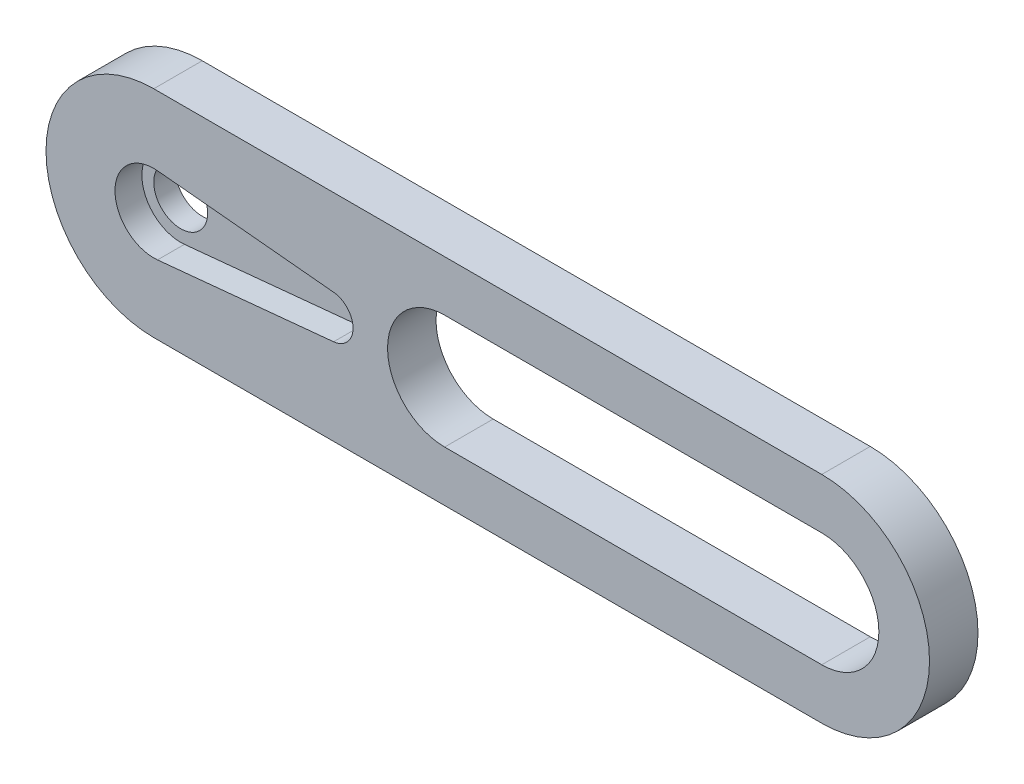
SolidWorks part; units mm, degrees
ref_plane "Front Plane" through (0, 0, 0) normal (0, 0, 1) x (1, 0, 0)
ref_plane "Top Plane" through (0, 0, 0) normal (0, 1, 0) x (1, 0, 0)
ref_plane "Right Plane" through (0, 0, 0) normal (1, 0, 0) x (0, 0, -1)
sketch "Esquisse1" plane through (0, 0, 0) normal (0, 0, 1) x (1, 0, 0)
  line L0 (-3.6, 0) -> (-3.6, 5.3986) construction
  line L1 (0.3491, 3.583) -> (16.6939, 1.9906)
  line L2 (16.6939, -1.9906) -> (0.3491, -3.583)
  line L3 (18.5, 0) -> (18.5, 4.9554) construction
  line L4 (0, 10) -> (62, 10)
  line L5 (0, -10) -> (62, -10)
  line L6 (27, 0) -> (62, 0) construction
  line L7 (27, 5.3) -> (62, 5.3)
  line L8 (27, -5.3) -> (62, -5.3)
  arc A0 (0.3491, 3.583) -> (0.3491, -3.583) centre (0, 0) ccw
  arc A1 (16.6939, -1.9906) -> (16.6939, 1.9906) centre (16.5, 0) ccw
  arc A2 (27, 5.3) -> (27, -5.3) centre (27, 0) ccw
  arc A3 (0, -10) -> (0, 10) centre (0, 0) cw
  arc A4 (62, 10) -> (62, -10) centre (62, 0) cw
  arc A5 (62, -5.3) -> (62, 5.3) centre (62, 0) ccw
  point P15 (44.5, 0)
  dimension "D2" = 3.6
  dimension "D3" = 2
  dimension "D5" = 35
  dimension "D6" = 10
  dimension "D8" = 10
  dimension "D4" = 5.3
  dimension "D1" = 22.1
  dimension "D7" = 62
extrude "Main" add sketch "Esquisse1" along normal blind 2.5
sketch "Esquisse2" plane through (0, 0, 0) normal (0, 0, -1) x (-1, 0, 0)
  line L0 (0, -10) -> (-62, -10)
  line L2 (0, -10) -> (-62, -10) construction
  line L3 (0, 10) -> (-62, 10)
  arc A0 (-62, 10) -> (-62, -10) centre (-62, 0) ccw construction
  circle A2 centre (0, 0) radius 2.5
  arc A3 (0, -10) -> (0, 10) centre (0, 0) ccw
  arc A5 (-62, 10) -> (-62, -10) centre (-62, 0) ccw
  dimension "D1" = 5
extrude "OriginalBracket" add sketch "Esquisse2" along normal blind 2
sketch "Sketch1" plane through (0, 0, 0) normal (0, 0, 1) x (1, 0, 0)
  line L0 (27, 0) -> (62, 0) construction
  line L1 (27, 5.3) -> (62, 5.3)
  line L2 (27, -5.3) -> (62, -5.3)
  arc A0 (27, 5.3) -> (27, -5.3) centre (27, 0) ccw
  arc A1 (62, -5.3) -> (62, 5.3) centre (62, 0) ccw
  point P4 (44.5, 0)
extrude "Cut-Extrude1" cut sketch "Sketch1" against normal through all
